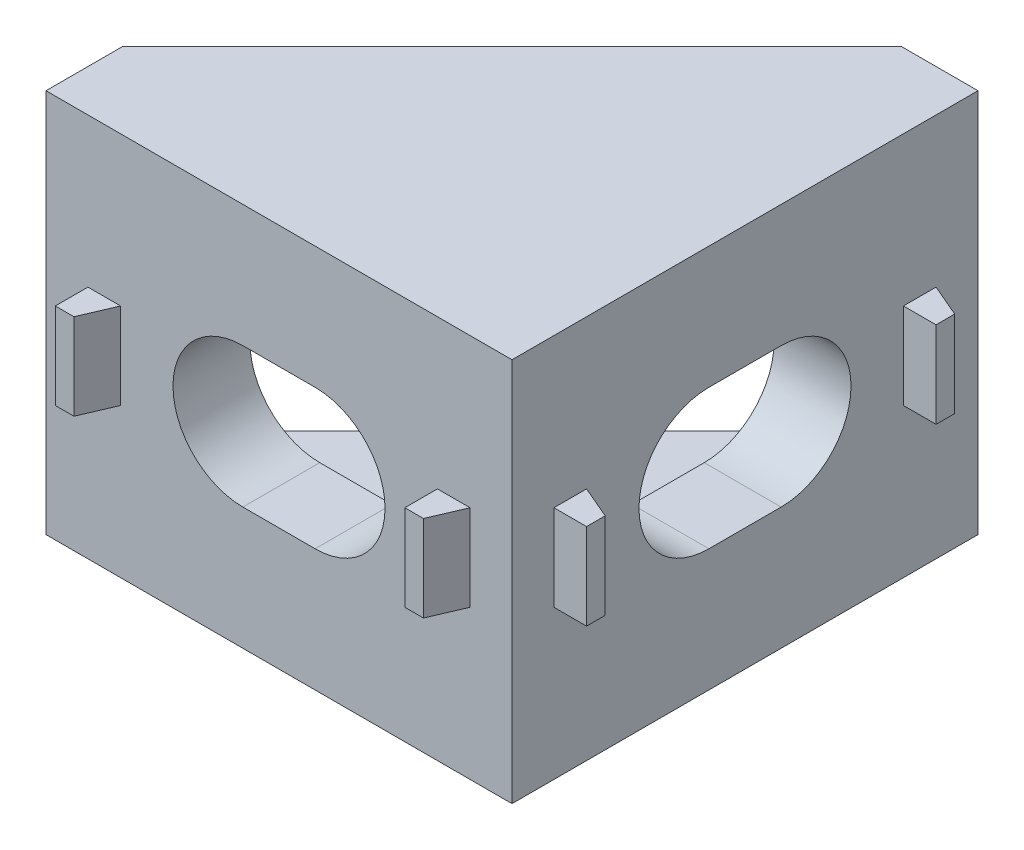
SolidWorks part; units mm, degrees
ref_plane "Alzado" through (0, 0, 0) normal (0, 0, 1) x (1, 0, 0)
ref_plane "Planta" through (0, 0, 0) normal (0, 1, 0) x (1, 0, 0)
ref_plane "Vista lateral" through (0, 0, 0) normal (1, 0, 0) x (0, 0, -1)
sketch "Croquis1" plane through (0, 0, 0) normal (0, 0, 1) x (1, 0, 0)
  line L0 (-1.55, 0) -> (1.55, 0) construction
  line L1 (-10, -8.25) -> (10, -8.25)
  line L2 (-10, -8.25) -> (-10, 8.25)
  line L3 (-10, 8.25) -> (10, 8.25)
  line L4 (10, -8.25) -> (10, 8.25)
  line L5 (-10, -8.25) -> (10, 8.25) construction
  line L6 (-10, 8.25) -> (10, -8.25) construction
  line L7 (-1.55, 3) -> (1.55, 3)
  line L8 (-1.55, -3) -> (1.55, -3)
  arc A0 (-1.55, 3) -> (-1.55, -3) centre (-1.55, 0) ccw
  arc A1 (1.55, -3) -> (1.55, 3) centre (1.55, 0) ccw
  point P0 (0, 0)
  point P8 (0, 0)
  point P15 (-4.55, 0)
  point P16 (4.55, 0)
  dimension "D1" = 20
  dimension "D2" = 16.5
  dimension "D3" = 9.1
  dimension "D4" = 6
extrude "Saliente-Extruir1" add sketch "Croquis1" along normal blind 3.3
sketch "Croquis2" plane through (0, 0, 3.3) normal (0, 0, 1) x (1, 0, 0)
  line L0 (-10, 8.25) -> (-10, -8.25) construction
  line L1 (-8.2, -1.85) -> (-6.8, -1.85)
  line L2 (-8.2, -1.85) -> (-8.2, 1.85)
  line L3 (-8.2, 1.85) -> (-6.8, 1.85)
  line L4 (-6.8, -1.85) -> (-6.8, 1.85)
  line L5 (-8.2, -1.85) -> (-6.8, 1.85) construction
  line L6 (-8.2, 1.85) -> (-6.8, -1.85) construction
  line L7 (6.8, -1.85) -> (8.2, -1.85)
  line L8 (6.8, -1.85) -> (6.8, 1.85)
  line L9 (6.8, 1.85) -> (8.2, 1.85)
  line L10 (8.2, -1.85) -> (8.2, 1.85)
  line L11 (6.8, -1.85) -> (8.2, 1.85) construction
  line L12 (6.8, 1.85) -> (8.2, -1.85) construction
  line L13 (10, -8.25) -> (10, 8.25) construction
  point P0 (7.5, 0)
  point P3 (-7.5, 0)
  dimension "D1" = 1.8
  dimension "D2" = 1.8
  dimension "D3" = 1.4
  dimension "D4" = 1.4
  dimension "D5" = 3.7
  dimension "D6" = 3.7
extrude "Saliente-Extruir2" add sketch "Croquis2" along normal blind 1.4
sketch "Croquis4" plane through (0, -1.85, 0) normal (0, -1, 0) x (1, 0, 0)
  line L0 (8.2, 3.3) -> (7.6, 4.7)
  line L1 (6.8, 4.7) -> (8.2, 4.7) construction
  line L2 (7.6, 4.7) -> (8.2, 4.7)
  line L3 (8.2, 4.7) -> (8.2, 3.3)
  dimension "D1" = 0.8
extrude "Cortar-Extruir1" cut sketch "Croquis4" against normal up to vertex (3.7 mm away) up to point (8.2, 1.85, 3.3)
sketch "Croquis5" plane through (0, -1.85, 0) normal (0, -1, 0) x (1, 0, 0)
  line L0 (-6.8, 3.3) -> (-7.4, 4.7)
  line L1 (-8.2, 4.7) -> (-6.8, 4.7) construction
  line L2 (-7.4, 4.7) -> (-6.8, 4.7)
  line L3 (-6.8, 4.7) -> (-6.8, 3.3)
  dimension "D1" = 0.8
extrude "Cortar-Extruir2" cut sketch "Croquis5" against normal up to vertex (3.7 mm away)
ref_plane "Plano1" through (10, 0, 0) normal (1, 0, 0) x (0, 0, -1)
sketch "Croquis6" plane through (10, 0, 0) normal (1, 0, 0) x (0, 0, -1)
  line L0 (-3.3, 8.25) -> (16.7, 8.25)
  line L1 (-3.3, -8.25) -> (16.7, -8.25)
  line L2 (16.7, -8.25) -> (16.7, 8.25)
  line L3 (-3.3, 8.25) -> (-3.3, -8.25)
  line L4 (6.7, 16.5) -> (6.7, 0) construction
  line L5 (6.7, 0) -> (6.7, -8.25) construction
  line L6 (-13.3, 0) -> (6.7, 0) construction
  line L7 (6.7, 0) -> (16.7, 0) construction
  line L8 (5.15, 0) -> (8.25, 0) construction
  line L9 (5.15, 3) -> (8.25, 3)
  line L10 (5.15, -3) -> (8.25, -3)
  arc A0 (5.15, 3) -> (5.15, -3) centre (5.15, 0) ccw
  arc A1 (8.25, -3) -> (8.25, 3) centre (8.25, 0) ccw
  point P9 (6.7, 8.25)
  point P13 (-3.3, 0)
  point P15 (6.7, 0)
  point P22 (2.15, 0)
  point P23 (11.25, 0)
  dimension "D1" = 20
  dimension "D2" = 16.5
  dimension "D3" = 6
  dimension "D4" = 9.1
extrude "Saliente-Extruir3" add sketch "Croquis6" against normal blind 3.3
sketch "Croquis7" plane through (10, 0, 0) normal (1, 0, 0) x (0, 0, -1)
  line L0 (-3.3, -8.25) -> (-3.3, 8.25) construction
  line L1 (-1.5, -1.85) -> (-0.1, -1.85)
  line L2 (-1.5, -1.85) -> (-1.5, 1.85)
  line L3 (-1.5, 1.85) -> (-0.1, 1.85)
  line L4 (-0.1, -1.85) -> (-0.1, 1.85)
  line L5 (-1.5, -1.85) -> (-0.1, 1.85) construction
  line L6 (-1.5, 1.85) -> (-0.1, -1.85) construction
  line L7 (13.5, -1.85) -> (14.9, -1.85)
  line L8 (13.5, -1.85) -> (13.5, 1.85)
  line L9 (13.5, 1.85) -> (14.9, 1.85)
  line L10 (14.9, -1.85) -> (14.9, 1.85)
  line L11 (13.5, -1.85) -> (14.9, 1.85) construction
  line L12 (13.5, 1.85) -> (14.9, -1.85) construction
  line L13 (16.7, -8.25) -> (16.7, 8.25) construction
  line L14 (-2.5472, 0) -> (6.8472, 0) construction
  line L15 (6.8472, 0) -> (12.8633, 0) construction
  point P0 (-0.8, 0)
  point P5 (14.2, 0)
  point P16 (2.15, 0)
  dimension "D1" = 1.8
  dimension "D2" = 1.8
  dimension "D3" = 3.7
  dimension "D4" = 3.7
  dimension "D5" = 1.4
  dimension "D6" = 1.4
extrude "Saliente-Extruir4" add sketch "Croquis7" along normal blind 1.4
sketch "Croquis11" plane through (0, -1.85, 0) normal (0, -1, 0) x (1, 0, 0)
  line L0 (11.4, 0.1) -> (10, 0.1)
  line L1 (10, -9.075) -> (10, 9.075) construction
  line L2 (11.4, 0.1) -> (10, 0.1) construction
  line L3 (10, 0.1) -> (11.4, 0.7)
  line L4 (11.4, 1.5) -> (11.4, 0.1) construction
  line L5 (11.4, 0.7) -> (11.4, 0.1)
  dimension "D1" = 0.8
extrude "Cortar-Extruir3" cut sketch "Croquis11" against normal up to vertex (3.7 mm away)
sketch "Croquis12" plane through (0, -1.85, 0) normal (0, -1, 0) x (1, 0, 0)
  line L0 (11.4, -14.9) -> (10, -14.9)
  line L1 (10, -9.075) -> (10, 9.075) construction
  line L2 (11.4, -14.9) -> (10, -14.9) construction
  line L3 (10, -14.9) -> (11.4, -14.3)
  line L4 (11.4, -13.5) -> (11.4, -14.9) construction
  line L5 (11.4, -14.3) -> (11.4, -14.9)
  dimension "D1" = 0.8
extrude "Cortar-Extruir4" cut sketch "Croquis12" against normal up to vertex (3.7 mm away)
ref_plane "Plano3" through (0, -8.25, 0) normal (0, -1, 0) x (-1, 0, 0)
sketch "Croquis13" plane through (0, -8.25, 0) normal (0, -1, 0) x (-1, 0, 0)
  line L0 (-6.7, 16.7) -> (10, 0)
  line L1 (10, 0) -> (-6.7, 0)
  line L2 (-6.7, 0) -> (-6.7, 16.7)
extrude "Saliente-Extruir5" add sketch "Croquis13" against normal blind 2.2
ref_plane "Plano4" through (0, 8.25, 0) normal (0, 1, 0) x (1, 0, 0)
sketch "Croquis14" plane through (0, 8.25, 0) normal (0, 1, 0) x (1, 0, 0)
  line L0 (6.7, 16.7) -> (-10, 0)
  line L1 (-10, 0) -> (6.7, 0)
  line L2 (6.7, 0) -> (6.7, 16.7)
extrude "Saliente-Extruir6" add sketch "Croquis14" against normal blind 2.2
